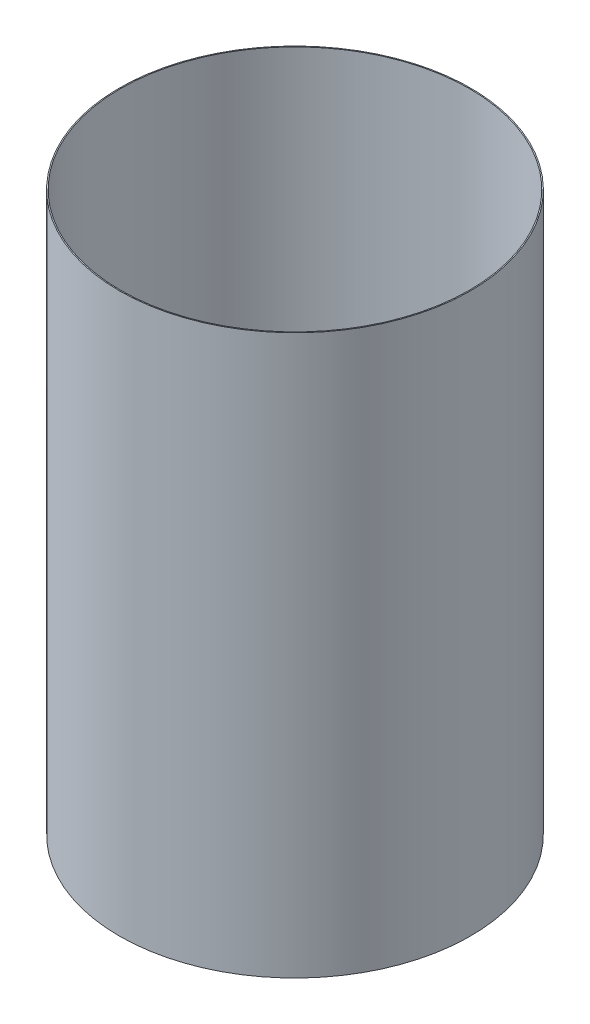
SolidWorks part; units mm, degrees
material "Thornel Mat VMA"
ref_plane "Front Plane" through (0, 0, 0) normal (0, 0, 1) x (1, 0, 0)
ref_plane "Top Plane" through (0, 0, 0) normal (0, 1, 0) x (1, 0, 0)
ref_plane "Right Plane" through (0, 0, 0) normal (1, 0, 0) x (0, 0, -1)
ref_axis "Axis1" through (0, 55, 0) along (0, -1, 0)
sketch "Sketch1" plane through (0, 0, 0) normal (0, 0, 1) x (1, 0, 0)
  line L0 (-41.656, -69.0032) -> (-41.656, -202.3532)
  line L2 (-38.1, -202.3532) -> (0, -202.3532) construction
  line L3 (-38.1, -69.0032) -> (0, -69.0032) construction
revolve "Revolve-Thin1" add sketch "Sketch1" angle 360 about axis through (0, 55, 0) along (0, -1, 0)
equation "\"D3@Revolve-Thin1\"=\"CF THICKNESS@Cryo Tank.Assembly\""
